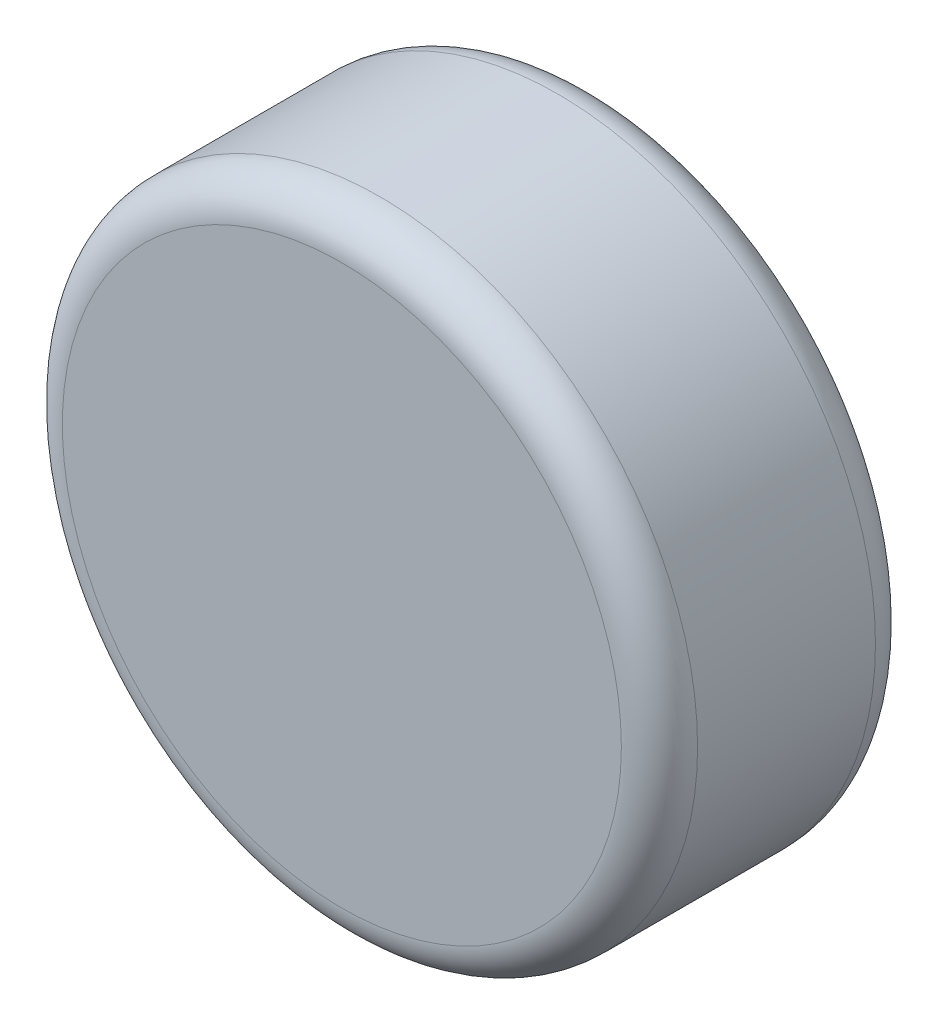
SolidWorks part; units mm, degrees
ref_plane "前视基准面" through (0, 0, 0) normal (0, 0, 1) x (1, 0, 0)
ref_plane "上视基准面" through (0, 0, 0) normal (0, 1, 0) x (1, 0, 0)
ref_plane "右视基准面" through (0, 0, 0) normal (1, 0, 0) x (0, 0, -1)
other "Configuration Table"
sketch "草图1" plane through (0, 0, 0) normal (0, 0, 1) x (1, 0, 0)
  circle A0 centre (0, 0) radius 2.5
  dimension "D1" = 5
extrude "凸台-拉伸1" add sketch "草图1" along normal blind 2
fillet "圆角1" radius 0.3 2 edges at (2.5, 0, 0) (2.5, 0, 2)
